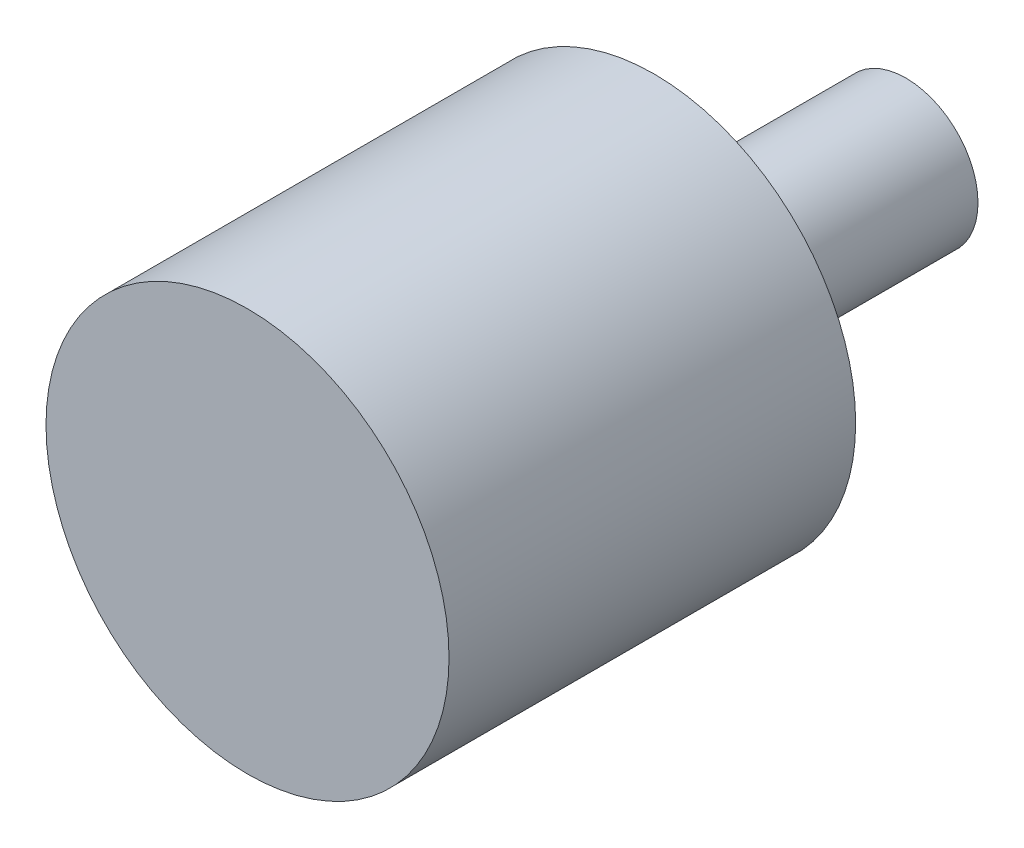
SolidWorks part; units mm, degrees
ref_plane "Front Plane" through (0, 0, 0) normal (0, 0, 1) x (1, 0, 0)
ref_plane "Top Plane" through (0, 0, 0) normal (0, 1, 0) x (1, 0, 0)
ref_plane "Right Plane" through (0, 0, 0) normal (1, 0, 0) x (0, 0, -1)
sketch "Sketch1" plane through (0, 0, 0) normal (0, 0, 1) x (1, 0, 0)
  circle A0 centre (0, 0) radius 28
  circle A1 centre (0, 0) radius 26
  dimension "D1" = 56
  dimension "D2" = 2
extrude "Boss-Extrude1" add sketch "Sketch1" along normal blind 55
sketch "Sketch2" plane through (0, 0, 55) normal (0, 0, 1) x (1, 0, 0)
  circle A0 centre (0, 0) radius 28 construction
  circle A1 centre (0, 0) radius 28
extrude "Boss-Extrude2" add sketch "Sketch2" along normal blind 1.5
sketch "Sketch3" plane through (0, 0, 55) normal (0, 0, -1) x (-1, 0, 0)
  circle A0 centre (0, 0) radius 10
  dimension "D1" = 20
extrude "Boss-Extrude3" add sketch "Sketch3" along normal blind 90
